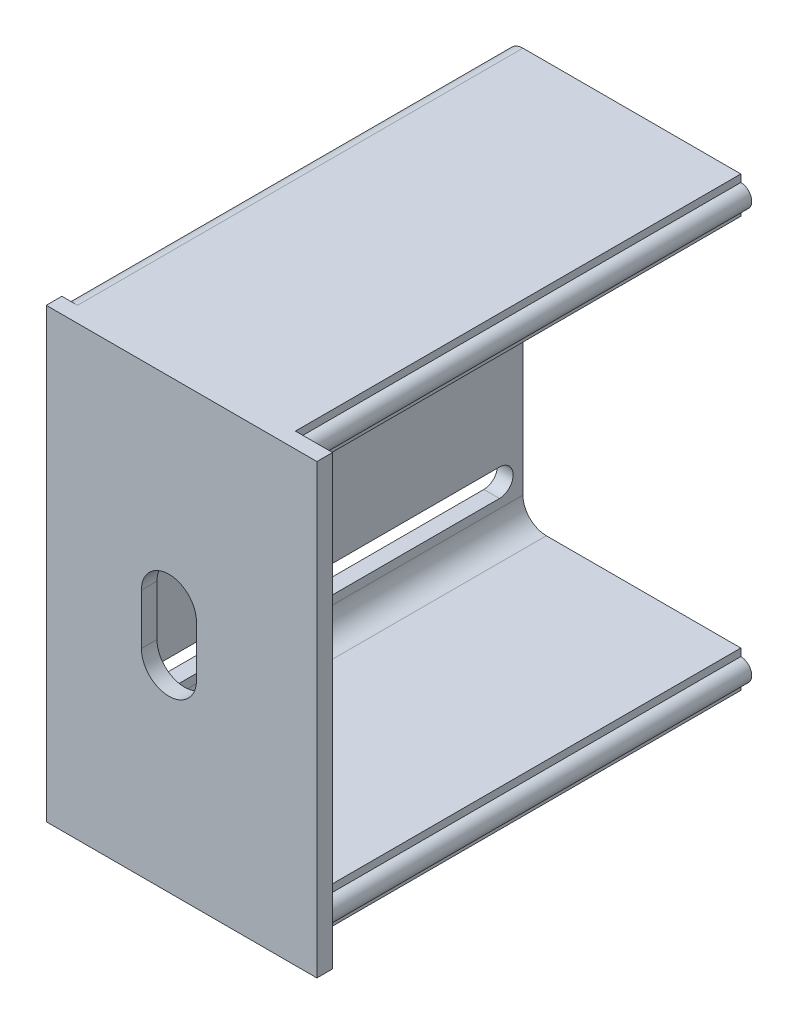
SolidWorks part; units mm, degrees
ref_plane "Alzado" through (0, 0, 0) normal (0, 0, 1) x (1, 0, 0)
ref_plane "Planta" through (0, 0, 0) normal (0, 1, 0) x (1, 0, 0)
ref_plane "Vista lateral" through (0, 0, 0) normal (1, 0, 0) x (0, 0, -1)
sketch "Croquis1" plane through (0, 0, 0) normal (0, 0, 1) x (1, 0, 0)
  line L1 (-1.5763, -3.4208) -> (-36.2135, -3.4208)
  line L2 (-1.5763, -3.4208) -> (-1.5763, 53.82)
  line L3 (-1.5763, 53.82) -> (-36.2135, 53.82)
  line L4 (-36.2135, -3.4208) -> (-36.2135, 53.82)
extrude "Saliente-Extruir1" add sketch "Croquis1" along normal blind 2
sketch "Croquis3" plane through (0, 0, 0) normal (0, 0, -1) x (-1, 0, 0)
  line L0 (6.3251, 52.8692) -> (6.3251, 53.82)
  line L1 (1.5763, 53.82) -> (36.2135, 53.82) construction
  line L2 (6.3251, 52.8692) -> (6.3251, 53.8208) construction
  line L3 (6.3251, 53.82) -> (34.2135, 53.82)
  line L8 (36.2135, 51.82) -> (36.2135, -1.4208)
  line L9 (34.2135, -3.4208) -> (6.3251, -3.4208)
  line L10 (36.2135, -3.4208) -> (1.5763, -3.4208) construction
  line L11 (6.3251, -3.4208) -> (6.3251, -2.4692) construction
  line L12 (6.3251, -3.4208) -> (6.3251, -2.4692)
  line L14 (6.3251, 0.3254) -> (6.3251, 1.2771)
  line L15 (6.3251, 1.2771) -> (31.2135, 1.2771)
  line L16 (6.3251, 50.0746) -> (6.3251, 49.1229)
  line L17 (6.3251, 49.1229) -> (31.2135, 49.1229)
  line L19 (34.2135, 46.1229) -> (34.2135, 4.2771)
  arc A0 (6.3251, 52.8692) -> (6.3251, 50.0746) centre (6.3251, 51.4719) ccw
  arc A1 (6.3251, 0.3254) -> (6.3251, -2.4692) centre (6.3251, -1.0719) ccw
  arc A2 (34.2135, 46.1229) -> (31.2135, 49.1229) centre (31.2135, 46.1229) ccw
  arc A3 (34.2135, 4.2771) -> (31.2135, 1.2771) centre (31.2135, 4.2771) cw
  arc A4 (34.2135, -3.4208) -> (36.2135, -1.4208) centre (34.2135, -1.4208) ccw
  arc A5 (36.2135, 51.82) -> (34.2135, 53.82) centre (34.2135, 51.82) ccw
  point P38 (36.2135, -3.4208)
  line M16 (1.5763, -3.4208) -> (36.2135, -3.4208)
  line M17 (36.2135, -3.4208) -> (36.2135, 53.82)
  line M18 (36.2135, 53.82) -> (1.5763, 53.82)
  dimension "D1" = 3
  dimension "D2" = 2
extrude "Saliente-Extruir2" add sketch "Croquis3" along normal up to surface (57 mm away) contours L19 A3 L15 L14 A1 L12 L3 L0 A0 L16 L17 A2 M16 M17 M18
sketch "Croquis4" plane through (-36.2135, 0, 0) normal (-1, 0, 0) x (0, 0, 1)
  line L0 (-57, -3.4208) -> (-57, 53.82) construction
  line L1 (-54, 43.25) -> (-5, 43.25) construction
  line L2 (-5, 43.25) -> (-54, 43.25) construction
  line L3 (-5, 41.5067) -> (-54, 41.5067)
  line L4 (-5, 44.9933) -> (-54, 44.9933)
  line L5 (-57, 25.1996) -> (11.1358, 25.1996) construction
  line L6 (-5, 7.1492) -> (-54, 7.1492) construction
  line L7 (-5, 8.8925) -> (-54, 8.8925)
  line L8 (-5, 5.4059) -> (-54, 5.4059)
  arc A0 (-5, 41.5067) -> (-5, 44.9933) centre (-5, 43.25) ccw
  arc A1 (-54, 44.9933) -> (-54, 41.5067) centre (-54, 43.25) ccw
  arc A2 (-5, 8.8925) -> (-5, 5.4059) centre (-5, 7.1492) cw
  arc A3 (-54, 5.4059) -> (-54, 8.8925) centre (-54, 7.1492) cw
  point P6 (-29.5, 43.25)
  point P17 (-29.5, 7.1492)
extrude "Cortar-Extruir1" cut sketch "Croquis4" against normal blind 3
sketch "Croquis5" plane through (-36.2135, 0, 0) normal (-1, 0, 0) x (0, 0, 1)
  line L0 (-12.75, 20.89) -> (-12.75, 29.51) construction
  line L1 (-13.25, 20.89) -> (-12.25, 20.89) construction
  line L2 (-12.25, 29.51) -> (-13.25, 29.51) construction
  line L3 (-12.75, 20.89) -> (-12.75, 29.51) construction
  line L4 (-14.3242, 20.89) -> (-14.3242, 29.51)
  line L5 (-11.1758, 20.89) -> (-11.1758, 29.51)
  arc A0 (-14.3242, 20.89) -> (-11.1758, 20.89) centre (-12.75, 20.89) ccw
  arc A1 (-11.1758, 29.51) -> (-14.3242, 29.51) centre (-12.75, 29.51) ccw
  point P6 (-12.75, 25.2)
extrude "Cortar-Extruir2" cut sketch "Croquis5" against normal blind 6
sketch "Croquis6" plane through (0, 0, 2) normal (0, 0, 1) x (1, 0, 0)
  line L0 (-20.5154, 21.8664) -> (-20.5154, 28.3369) construction
  line L1 (-24.0426, 21.8664) -> (-24.0426, 28.3369)
  line L2 (-16.9883, 21.8664) -> (-16.9883, 28.3369)
  arc A0 (-24.0426, 21.8664) -> (-16.9883, 21.8664) centre (-20.5154, 21.8664) ccw
  arc A1 (-16.9883, 28.3369) -> (-24.0426, 28.3369) centre (-20.5154, 28.3369) ccw
  point P2 (-20.5154, 25.1017)
extrude "Cortar-Extruir3" cut sketch "Croquis6" against normal up to next
